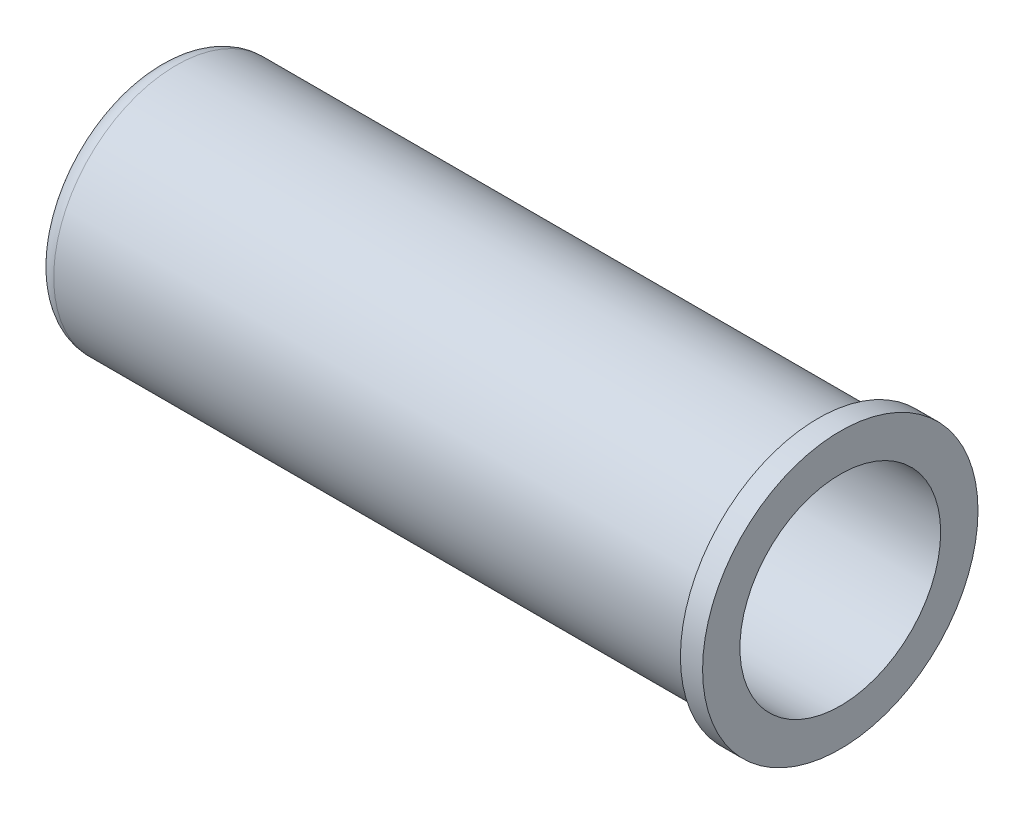
SolidWorks part; units mm, degrees
material "Acier allié inoxydable"
ref_plane "Plan de face" through (0, 0, 0) normal (0, 0, 1) x (1, 0, 0)
ref_plane "Plan de dessus" through (0, 0, 0) normal (0, 1, 0) x (1, 0, 0)
ref_plane "Plan de droite" through (0, 0, 0) normal (1, 0, 0) x (0, 0, -1)
sketch "Esquisse1" plane through (0, 0, 0) normal (0, 0, 1) x (1, 0, 0)
  line L0 (0, 0) -> (-10, 0) construction
  line L1 (0, 4.3) -> (-27.5, 4.3)
  line L2 (-28.3, 3.5) -> (-28.3, 3.35)
  line L3 (-28.3, 3.35) -> (-29.25, 3.35)
  line L4 (-29.25, 3.35) -> (-29.25, 4.45)
  line L5 (-28.45, 5.25) -> (-0.95, 5.25)
  line L6 (0, 5.25) -> (0, 4.3)
  line L7 (0, 4.3) -> (0, 0) construction
  line L8 (0, 5.25) -> (0, 5.9)
  line L9 (0, 5.9) -> (-0.95, 5.9)
  line L10 (-0.95, 5.9) -> (-0.95, 5.25)
  line L11 (-0.95, 5.25) -> (0, 5.25) construction
  arc A0 (-29.25, 4.45) -> (-28.45, 5.25) centre (-28.45, 4.45) cw
  arc A1 (-27.5, 4.3) -> (-28.3, 3.5) centre (-27.5, 3.5) ccw
  point P13 (-28.3, 4.3)
  dimension "D6" = 0.8
  dimension "D8" = 0.8
  dimension "D1" = 10
  dimension "D2" = 4.3
  dimension "D3" = 0.95
  dimension "D4" = 0.95
  dimension "D5" = 0.95
  dimension "D7" = 29.25
  dimension "D9" = 5.9
  dimension "D10" = 0.95
revolve "Révolution1" add sketch "Esquisse1" angle 360 about L0
